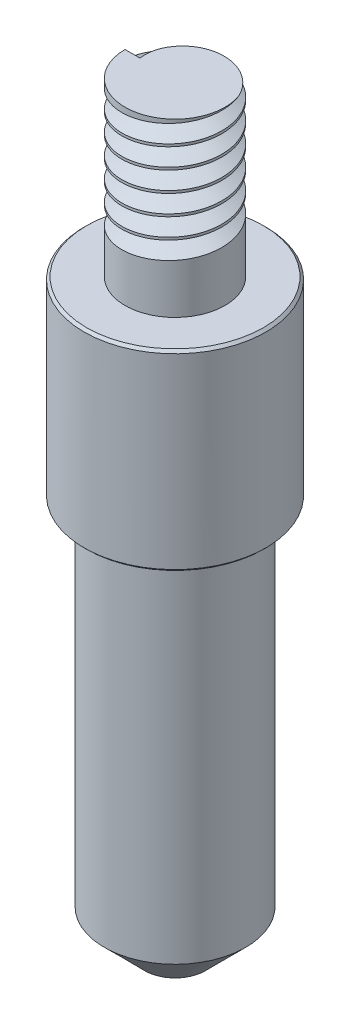
SolidWorks part; units mm, degrees
ref_plane "Front Plane" through (0, 0, 0) normal (0, 0, 1) x (1, 0, 0)
ref_plane "Top Plane" through (0, 0, 0) normal (0, 1, 0) x (1, 0, 0)
ref_plane "Right Plane" through (0, 0, 0) normal (1, 0, 0) x (0, 0, -1)
sketch "Sketch1" plane through (0, 0, 0) normal (0, 0, 1) x (1, 0, 0)
  line L0 (0, 0) -> (0, 75) construction
  line L1 (9, 39) -> (9, 58)
  line L2 (7, 4) -> (7, 39)
  line L3 (0, 0) -> (3, 0)
  line L4 (7, 39) -> (9, 39)
  line L5 (4.95, 58) -> (9, 58)
  line L7 (9, 0) -> (9, 75) construction
  line L8 (0, 0) -> (9, 0) construction
  line L9 (3, 0) -> (7, 4)
  line L10 (7, 0) -> (7, 75) construction
  line L11 (0, 39) -> (9, 39) construction
  line L12 (0, 58) -> (9, 58) construction
  line L13 (0, 75) -> (4.95, 75)
  line L14 (4.95, 58) -> (4.95, 75)
  line L15 (0, 0) -> (0, 75)
  point P17 (5, 0)
  dimension "D2" = 75
  dimension "D1" = 9
  dimension "D3" = 7
  dimension "D4" = 39
  dimension "D5" = 19
revolve "Revolve1" add sketch "Sketch1" angle 360 about L15
sketch "Sketch2" plane through (0, 75, 0) normal (0, 1, 0) x (1, 0, 0)
  circle A0 centre (0, 0) radius 5
  dimension "D1" = 10
curve "Helix/Spiral1" pitch 2 height 12 turns 6
ref_plane "Plane1" through (-5, 75, 0) normal (0, -0.0635, -0.998) x (-1, 0, 0)
sketch "Sketch3" plane through (-5, 75, 0) normal (0, -0.0635, -0.998) x (-1, 0, 0)
  line L1 (-1.5619, -0.0207) -> (0.6272, -1.2292)
  line L2 (0.6272, -1.2292) -> (0.5792, 1.2708)
  line L3 (0.5792, 1.2708) -> (-1.5619, -0.0207)
  circle A0 centre (-0.1185, 0.0069) radius 0.7218 construction
  dimension "D1" = 2.5
chamfer "Chamfer1" distance 0.25 angle 45 1 edges at (0, 58, -9)
chamfer "Chamfer2" distance 0.25 angle 45 1 edges at (0, 39, -9)
sweep "Cut-Sweep2" cut profiles "Sketch3" path "Helix/Spiral1"
